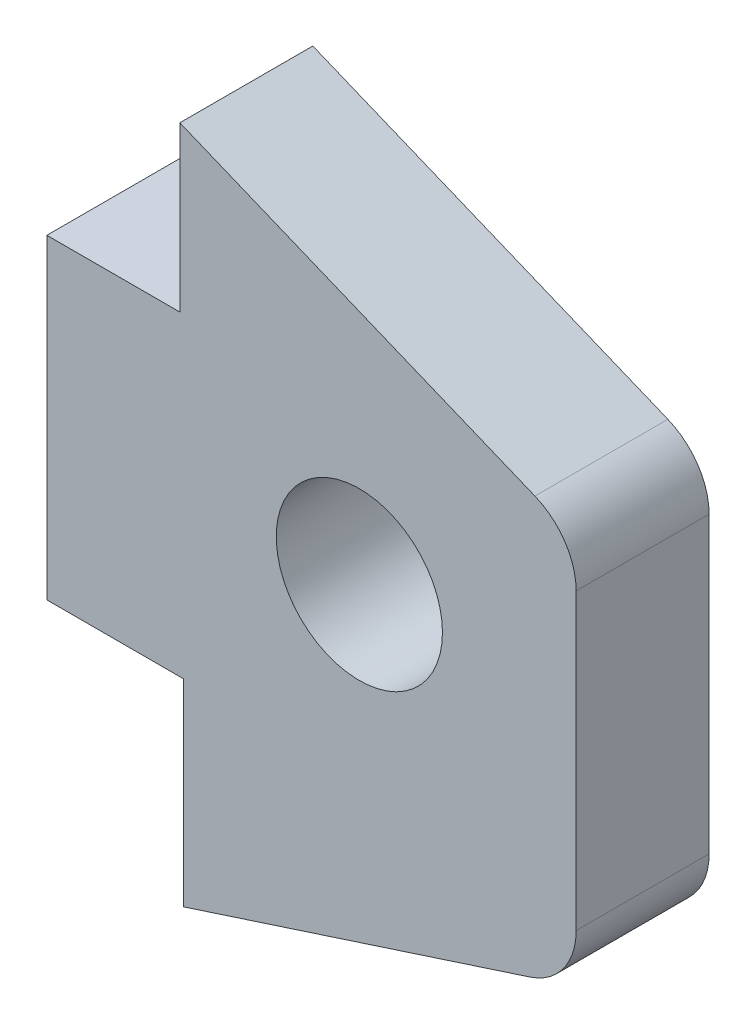
SolidWorks part; units mm, degrees
ref_plane "正面" through (0, 0, 0) normal (0, 0, 1) x (1, 0, 0)
ref_plane "平面" through (0, 0, 0) normal (0, 1, 0) x (1, 0, 0)
ref_plane "右側面" through (0, 0, 0) normal (1, 0, 0) x (0, 0, -1)
sketch "ｽｹｯﾁ1" plane through (0, 0, 0) normal (0, 0, 1) x (1, 0, 0)
  line L0 (0, 0) -> (0, -9.5)
  line L1 (0, -9.5) -> (4.1073, -9.5)
  line L2 (4.1073, -9.5) -> (4.1073, -15.4415)
  line L3 (4.1073, -15.4415) -> (15.9224, -11.6074)
  line L4 (15.9224, -11.6074) -> (15.9224, 0.0374)
  line L5 (15.9224, 0.0374) -> (4, 4.9307)
  line L6 (4, 4.9307) -> (4, 0)
  line L7 (4, 0) -> (0, 0)
  line L8 (9.4, 2.7144) -> (9.4, -13.724) construction
  circle A0 centre (9.4, -4.4) radius 2.5
  dimension "D4" = 5
  dimension "D1" = 4
  dimension "D2" = 9.5
  dimension "D3" = 9.4
  dimension "D5" = 4.1073
  dimension "D6" = 15.9224
  dimension "D7" = 0.0374
  dimension "D8" = 4.9307
  dimension "D9" = 4.4
  dimension "D10" = 11.6074
  dimension "D11" = 15.4415
extrude "ﾎﾞｽ - 押し出し1" add sketch "ｽｹｯﾁ1" along normal blind 4
fillet "ﾌｨﾚｯﾄ1" radius 2 2 edges at (15.9224, -11.6074, 2) (15.9224, 0.0374, 2)
